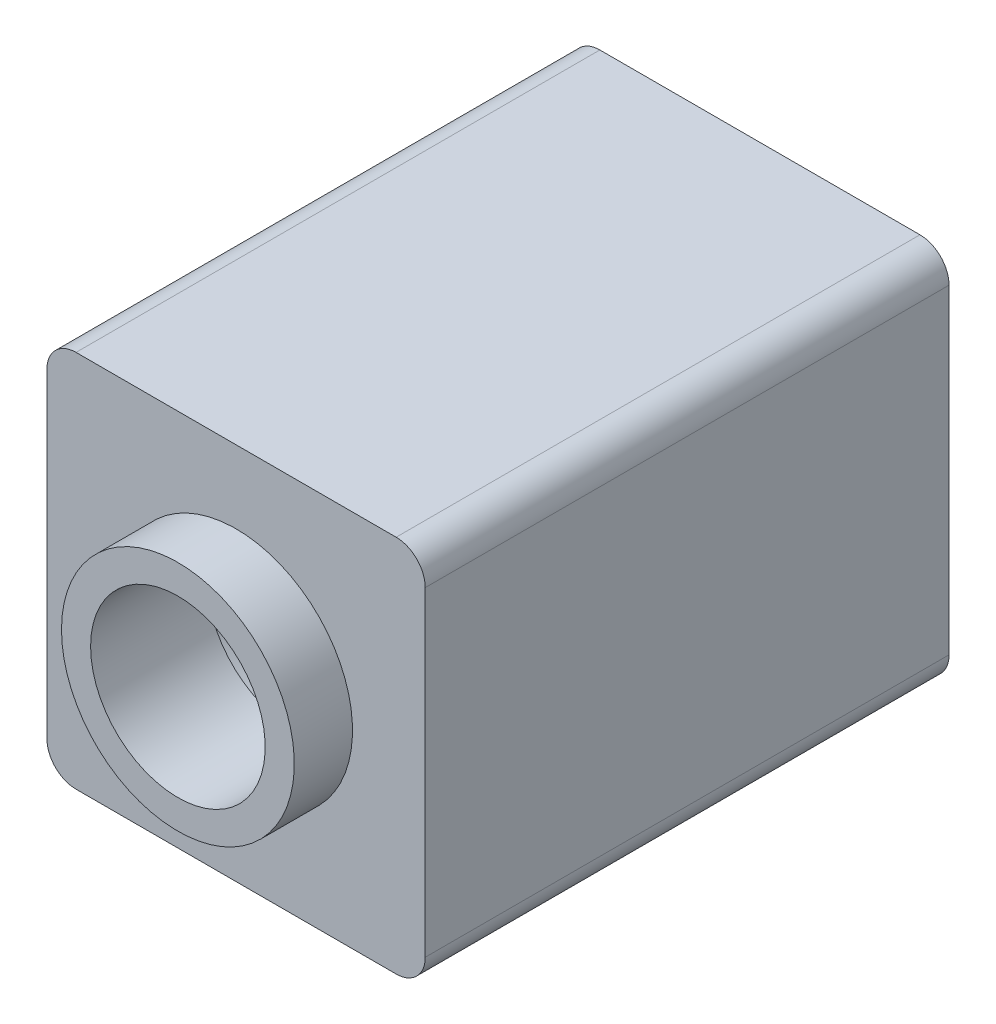
SolidWorks part; units mm, degrees
ref_plane "Front Plane" through (0, 0, 0) normal (0, 0, 1) x (1, 0, 0)
ref_plane "Top Plane" through (0, 0, 0) normal (0, 1, 0) x (1, 0, 0)
ref_plane "Right Plane" through (0, 0, 0) normal (1, 0, 0) x (0, 0, -1)
sketch "Sketch2" plane through (0, 0, -57.4655) normal (0, 0, -1) x (-1, 0, 0)
  line L1 (-6.4905, -35.0784) -> (-0.9905, -35.0784)
  line L2 (-6.9905, -34.5784) -> (-6.9905, -29.0784)
  line L3 (-6.4905, -28.5784) -> (-0.9905, -28.5784)
  line L4 (-0.4905, -34.5784) -> (-0.4905, -29.0784)
  line L5 (-6.9905, -35.0784) -> (-0.4905, -28.5784) construction
  line L6 (-6.9905, -28.5784) -> (-0.4905, -35.0784) construction
  circle A0 centre (-3.7405, -31.8284) radius 1.5
  arc A1 (-0.4905, -34.5784) -> (-0.9905, -35.0784) centre (-0.9905, -34.5784) cw
  arc A2 (-6.9905, -34.5784) -> (-6.4905, -35.0784) centre (-6.4905, -34.5784) ccw
  arc A3 (-6.9905, -29.0784) -> (-6.4905, -28.5784) centre (-6.4905, -29.0784) cw
  arc A4 (-0.4905, -29.0784) -> (-0.9905, -28.5784) centre (-0.9905, -29.0784) ccw
  point P0 (-3.7405, -31.8284)
  dimension "D2" = 3
  dimension "D3" = 0.5
  dimension "D1" = 6.5
extrude "Boss-Extrude1" add sketch "Sketch2" along normal blind 10
sketch "Sketch3" plane through (0, 0, -57.4655) normal (0, 0, -1) x (-1, 0, 0)
  line L4 (-0.9905, -28.5784) -> (-6.4905, -28.5784)
  line L5 (-6.9905, -29.0784) -> (-6.9905, -34.5784)
  line L6 (-6.4905, -35.0784) -> (-0.9905, -35.0784)
  line L7 (-0.4905, -34.5784) -> (-0.4905, -29.0784)
  line L8 (-0.9905, -28.5784) -> (-6.4905, -28.5784)
  line L9 (-6.9905, -29.0784) -> (-6.9905, -34.5784)
  line L10 (-6.4905, -35.0784) -> (-0.9905, -35.0784)
  line L11 (-0.4905, -34.5784) -> (-0.4905, -29.0784)
  circle A1 centre (-3.7405, -31.8284) radius 5 construction
  circle A2 centre (-3.7405, -31.8284) radius 2
  arc A6 (-6.4905, -28.5784) -> (-6.9905, -29.0784) centre (-6.4905, -29.0784) ccw
  arc A7 (-6.9905, -34.5784) -> (-6.4905, -35.0784) centre (-6.4905, -34.5784) ccw
  arc A8 (-0.9905, -35.0784) -> (-0.4905, -34.5784) centre (-0.9905, -34.5784) ccw
  arc A9 (-0.4905, -29.0784) -> (-0.9905, -28.5784) centre (-0.9905, -29.0784) ccw
  arc A10 (-6.4905, -28.5784) -> (-6.9905, -29.0784) centre (-6.4905, -29.0784) ccw
  arc A11 (-6.9905, -34.5784) -> (-6.4905, -35.0784) centre (-6.4905, -34.5784) ccw
  arc A12 (-0.9905, -35.0784) -> (-0.4905, -34.5784) centre (-0.9905, -34.5784) ccw
  arc A13 (-0.4905, -29.0784) -> (-0.9905, -28.5784) centre (-0.9905, -29.0784) ccw
  dimension "D1" = 4
  dimension "D2" = 0
extrude "Cut-Extrude1" cut sketch "Sketch3" along normal blind 1
sketch "Sketch4" plane through (0, 0, -67.4655) normal (0, 0, -1) x (-1, 0, 0)
  circle A0 centre (-3.7405, -31.8284) radius 2.4
extrude "Cut-Extrude2" cut sketch "Sketch4" against normal blind 8
